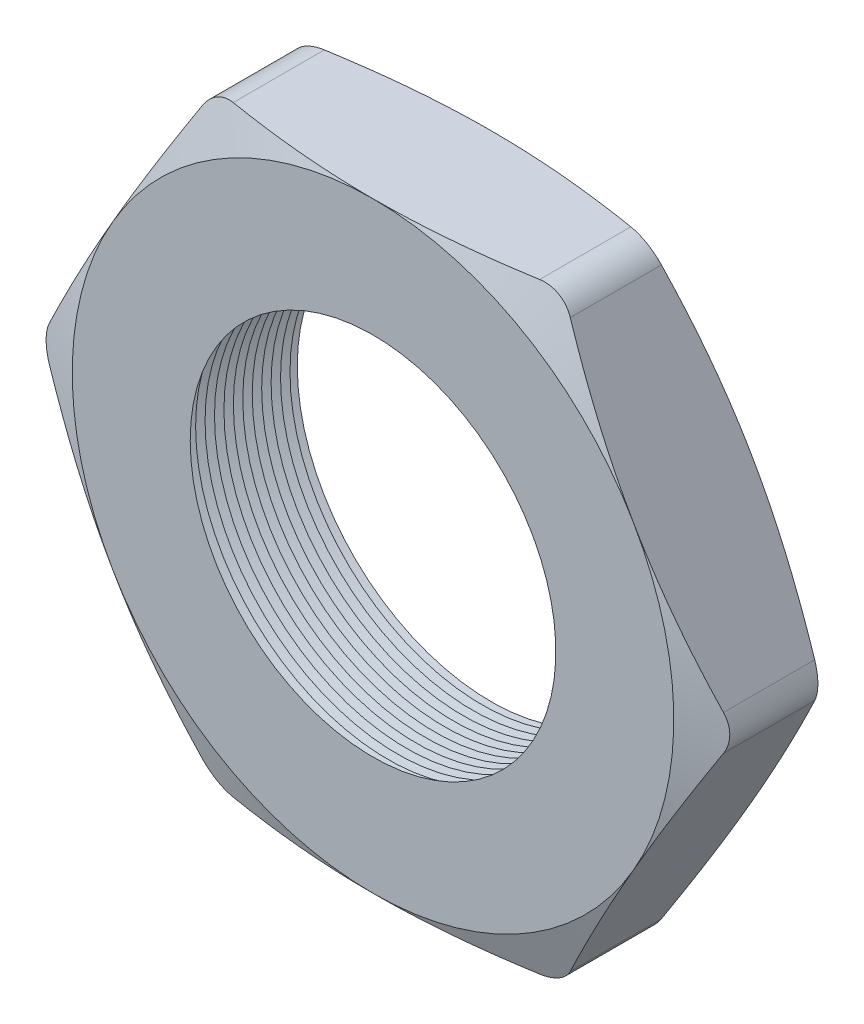
SolidWorks part; units mm, degrees
ref_plane "Front Plane" through (0, 0, 0) normal (0, 0, 1) x (1, 0, 0)
ref_plane "Top Plane" through (0, 0, 0) normal (0, 1, 0) x (1, 0, 0)
ref_plane "Right Plane" through (0, 0, 0) normal (1, 0, 0) x (0, 0, -1)
sketch "Sketch1" plane through (0, 0, 0) normal (0, 0, 1) x (1, 0, 0)
  line L1 (-7.479, 0) -> (-3.7395, -6.477)
  line L2 (-3.7395, -6.477) -> (3.7395, -6.477)
  line L3 (3.7395, -6.477) -> (7.479, 0)
  line L4 (7.479, 0) -> (3.7395, 6.477)
  line L5 (3.7395, 6.477) -> (-3.7395, 6.477)
  line L6 (-3.7395, 6.477) -> (-7.479, 0)
  circle A0 centre (0, 0) radius 6.477 construction
  circle A1 centre (0, 0) radius 3.937
  dimension "TS" = 7.874
  dimension "H" = 12.954
extrude "Extrude1" add sketch "Sketch1" along normal blind 2.54
fillet "Fillet1" radius 0.762 6 edges at (-3.7395, 6.477, 1.27) (-7.479, 0, 1.27) (-3.7395, -6.477, 1.27) (3.7395, -6.477, 1.27) (7.479, 0, 1.27) (3.7395, 6.477, 1.27)
sketch "Sketch2" plane through (0, 0, 2.54) normal (0, 0, 1) x (1, 0, 0)
  line L0 (3.2996, 6.477) -> (-3.2996, 6.477) construction
  circle A0 centre (0, 0) radius 6.477
extrude "Cut-Extrude1" cut sketch "Sketch2" against normal through all draft 70 flip side to cut
sketch "Sketch3" plane through (0, 0, 0) normal (0, 0, -1) x (-1, 0, 0)
  circle A0 centre (0, 0) radius 6.477
extrude "Cut-Extrude2" cut sketch "Sketch3" against normal through all draft 70 flip side to cut
sketch "Sketch4" plane through (0, 0, 0) normal (0, 1, 0) x (1, 0, 0)
  line L0 (-3.937, -2.54) -> (-3.937, -2.1001)
  line L2 (-3.937, -2.1001) -> (-4.318, -2.32)
  line L3 (-4.318, -2.32) -> (-3.937, -2.54)
  line L5 (-3.937, 0) -> (-3.937, -2.54) construction
  line L6 (-3.937, -2.54) -> (3.937, -2.54) construction
  dimension "D1" = 60
  dimension "D2" = 60
  dimension "D3" = 0.381
revolve "Cut-Revolve1" cut sketch "Sketch4" angle 360 about axis through (0, 0, 2.54) along (0, 0, -1)
pattern_linear "LPattern1" count 13 spacing 0.2032 along (0, 0, -1) of "Cut-Revolve1"
